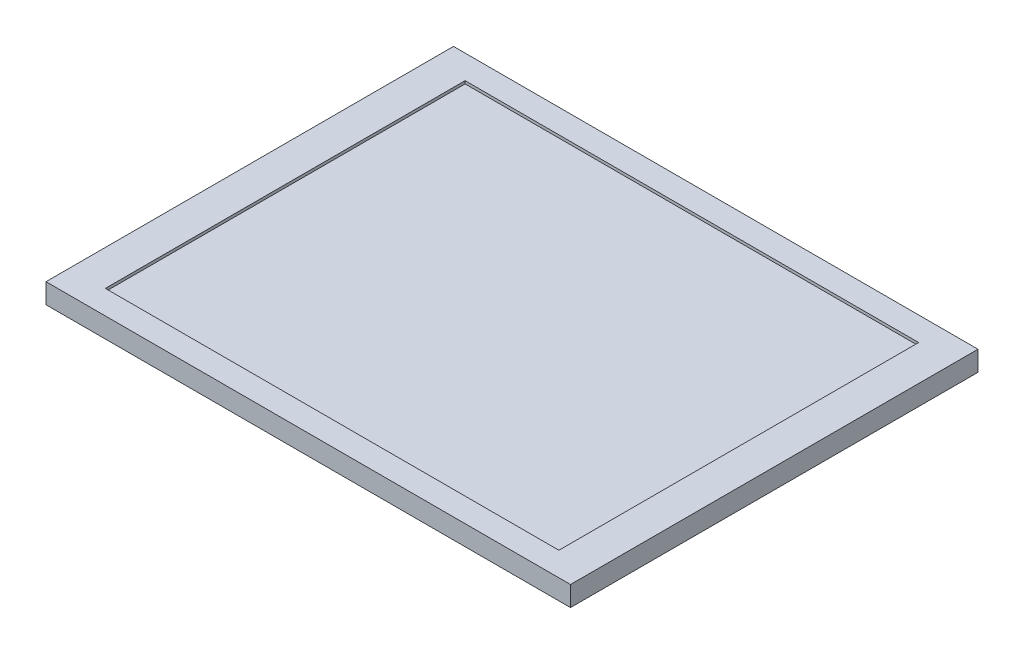
SolidWorks part; units mm, degrees
ref_plane "Plano frontal" through (0, 0, 0) normal (0, 0, 1) x (1, 0, 0)
ref_plane "Plano superior" through (0, 0, 0) normal (0, 1, 0) x (1, 0, 0)
ref_plane "Plano direito" through (0, 0, 0) normal (1, 0, 0) x (0, 0, -1)
sketch "Esboço1" plane through (0, 0, 0) normal (0, 1, 0) x (1, 0, 0)
  line L1 (-139, 108) -> (139, 108)
  line L2 (-139, 108) -> (-139, -108)
  line L3 (-139, -108) -> (139, -108)
  line L4 (139, 108) -> (139, -108)
  line L5 (-139, 108) -> (139, -108) construction
  line L6 (-139, -108) -> (139, 108) construction
  point P0 (0, 0)
  dimension "D1" = 278
  dimension "D2" = 216
extrude "Ressalto-extrusão1" add sketch "Esboço1" along normal blind 9.1
sketch "Esboço2" plane through (0, 9.1, 0) normal (0, 1, 0) x (1, 0, 0)
  line L0 (-139, -108) -> (139, -108) construction
  line L1 (-139, 108) -> (-120.2, 108)
  line L2 (-139, 108) -> (-139, -108)
  line L3 (-139, -108) -> (-120.2, -108)
  line L4 (-120.2, 95.35) -> (-120.2, -95.35)
  line L7 (139, -108) -> (120.2, -108)
  line L8 (120.2, 95.35) -> (120.2, -95.35)
  line L9 (139, 108) -> (120.2, 108)
  line L10 (139, 108) -> (139, -108)
  line L11 (-120.2, 108) -> (120.2, 108)
  line L13 (-120.2, 95.35) -> (120.2, 95.35)
  line L15 (-120.2, -95.35) -> (120.2, -95.35)
  line L17 (-120.2, -108) -> (120.2, -108)
  dimension "D1" = 18.8
extrude "Ressalto-extrusão2" add sketch "Esboço2" along normal blind 1.5
